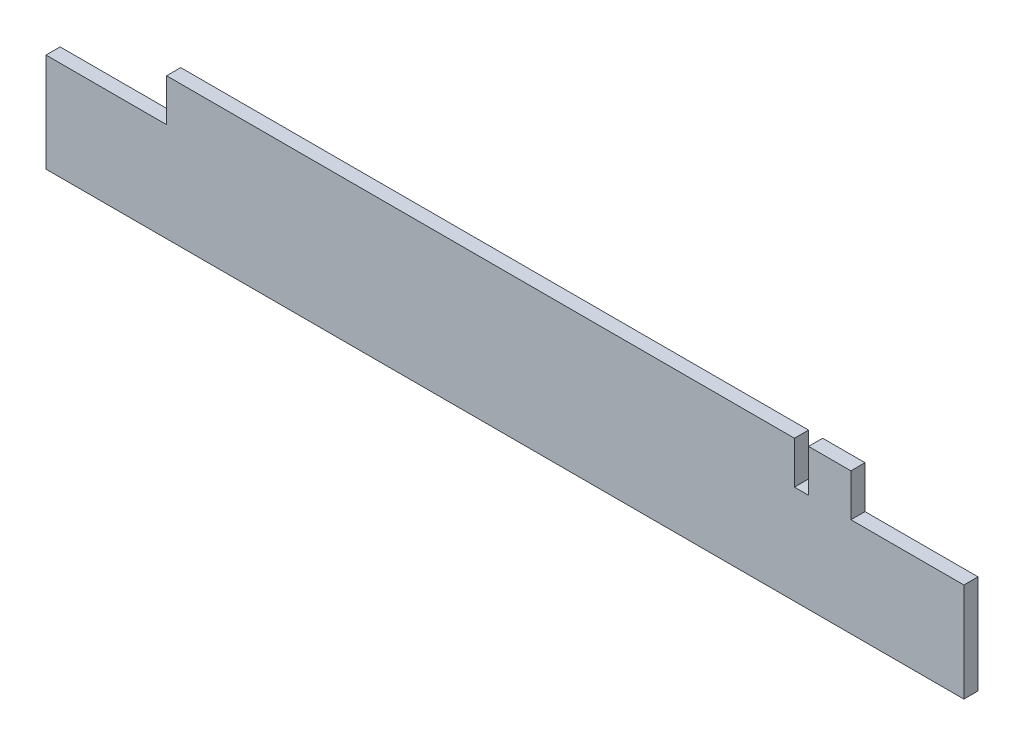
SolidWorks part; units mm, degrees
ref_plane "Plan de face" through (0, 0, 0) normal (0, 0, 1) x (1, 0, 0)
ref_plane "Plan de dessus" through (0, 0, 0) normal (0, 1, 0) x (1, 0, 0)
ref_plane "Plan de droite" through (0, 0, 0) normal (1, 0, 0) x (0, 0, -1)
sketch "Esquisse1" plane through (0, 0, 0) normal (0, 0, 1) x (1, 0, 0)
  line L5 (-325, -219.4526) -> (325, -219.4526)
  line L6 (-325, -219.4526) -> (-325, -119.4526)
  line L7 (-325, -119.4526) -> (325, -119.4526)
  line L8 (325, -219.4526) -> (325, -119.4526)
  line L9 (-325, -219.4526) -> (325, -119.4526) construction
  line L10 (-325, -119.4526) -> (325, -219.4526) construction
  line L11 (-325, -119.4526) -> (-239.5985, -119.4526)
  line L12 (-325, -119.4526) -> (-325, -149.4526)
  line L13 (-325, -149.4526) -> (-239.5985, -149.4526)
  line L14 (-239.5985, -119.4526) -> (-239.5985, -149.4526)
  line L15 (325, -119.4526) -> (245, -119.4526)
  line L16 (325, -119.4526) -> (325, -149.4526)
  line L17 (325, -149.4526) -> (245, -149.4526)
  line L18 (245, -119.4526) -> (245, -149.4526)
  dimension "D1" = 650
  dimension "D2" = 100
  dimension "D3" = 80
  dimension "D4" = 30
  dimension "D5" = 30
extrude "Boss.-Extru.1" add sketch "Esquisse1" along normal blind 10 contours L18 L7 L14 L13 L6 L5 L8 L17
sketch "Esquisse2" plane through (0, 0, 0) normal (0, 0, -1) x (-1, 0, 0)
  line L0 (239.5985, -119.4526) -> (-245, -119.4526) construction
  line L1 (-215, -119.4526) -> (-205, -119.4526)
  line L2 (-215, -119.4526) -> (-215, -149.4526)
  line L3 (-215, -149.4526) -> (-205, -149.4526)
  line L4 (-205, -119.4526) -> (-205, -149.4526)
  line L5 (-245, -119.4526) -> (-245, -149.4526) construction
  dimension "D1" = 10
  dimension "D2" = 0
  dimension "D3" = 30
extrude "Enlèv. mat.-Extru.1" cut sketch "Esquisse2" against normal through all
